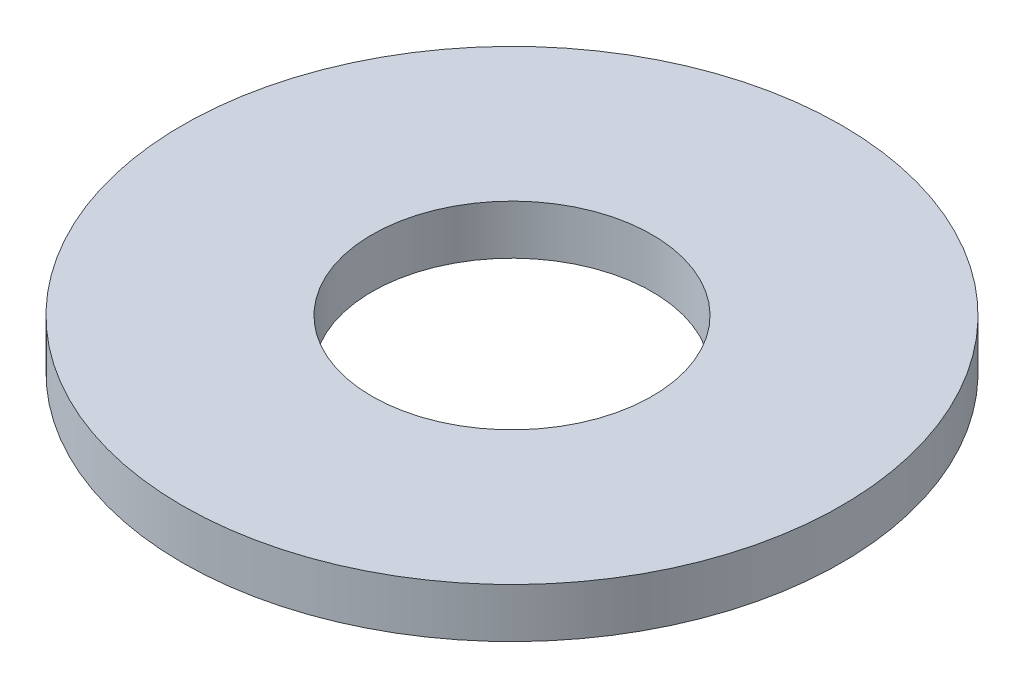
SolidWorks part; units mm, degrees
material "Plain Carbon Steel"
ref_plane "Front" through (0, 0, 0) normal (0, 0, 1) x (1, 0, 0)
ref_plane "Top" through (0, 0, 0) normal (0, 1, 0) x (1, 0, 0)
ref_plane "Right" through (0, 0, 0) normal (1, 0, 0) x (0, 0, -1)
sketch "Sketch1" plane through (0, 0, 0) normal (0, 1, 0) x (1, 0, 0)
  circle A0 centre (0, 0) radius 17
  circle A1 centre (0, 0) radius 40
  dimension "D1" = 34
  dimension "D2" = 80
extrude "Boss-Extrude1" add sketch "Sketch1" along normal blind 6
